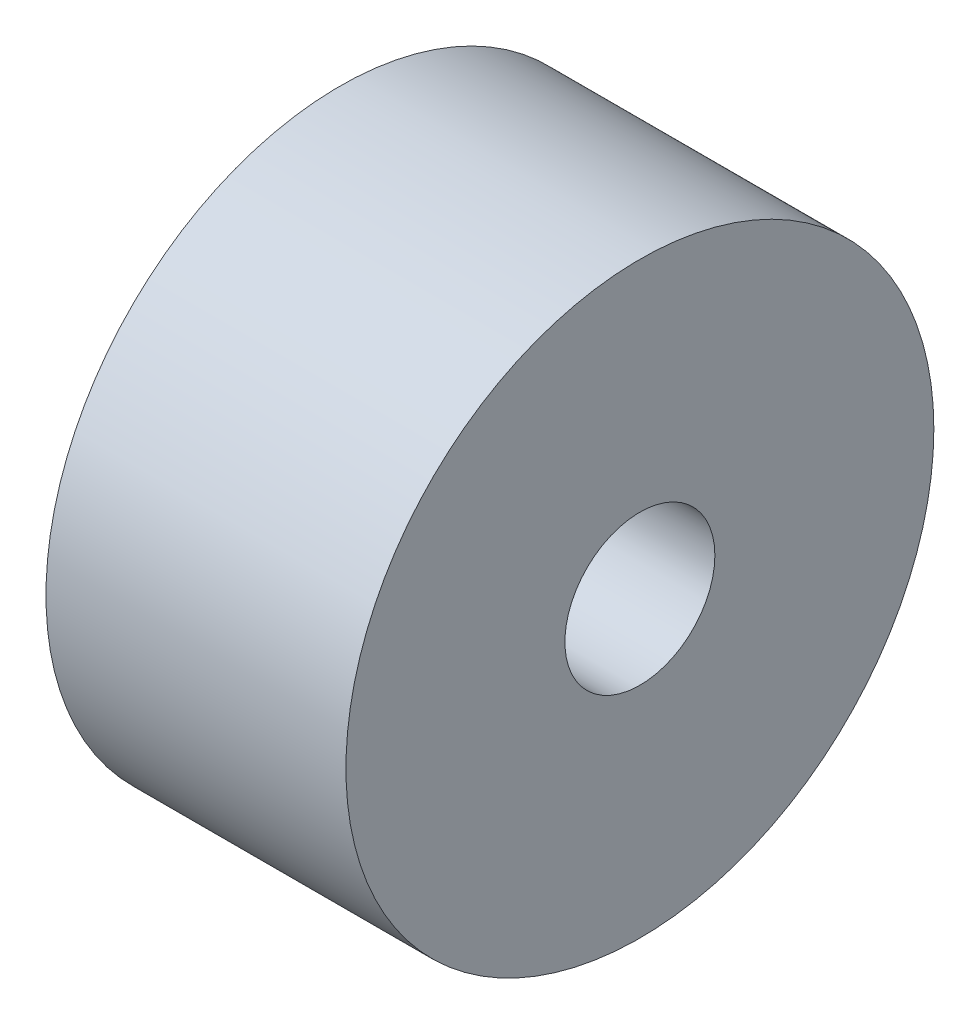
SolidWorks part; units mm, degrees
material "PVC Rigid"
ref_plane "Front Plane" through (0, 0, 0) normal (0, 0, 1) x (1, 0, 0)
ref_plane "Top Plane" through (0, 0, 0) normal (0, 1, 0) x (1, 0, 0)
ref_plane "Right Plane" through (0, 0, 0) normal (1, 0, 0) x (0, 0, -1)
sketch "Sketch1" plane through (0, 0, 0) normal (1, 0, 0) x (0, 0, -1)
  circle A0 centre (0, 0) radius 49
  circle A1 centre (0, 0) radius 12.5
  dimension "D1" = 25
  dimension "D2" = 98
extrude "Boss-Extrude1" add sketch "Sketch1" along normal blind 50
